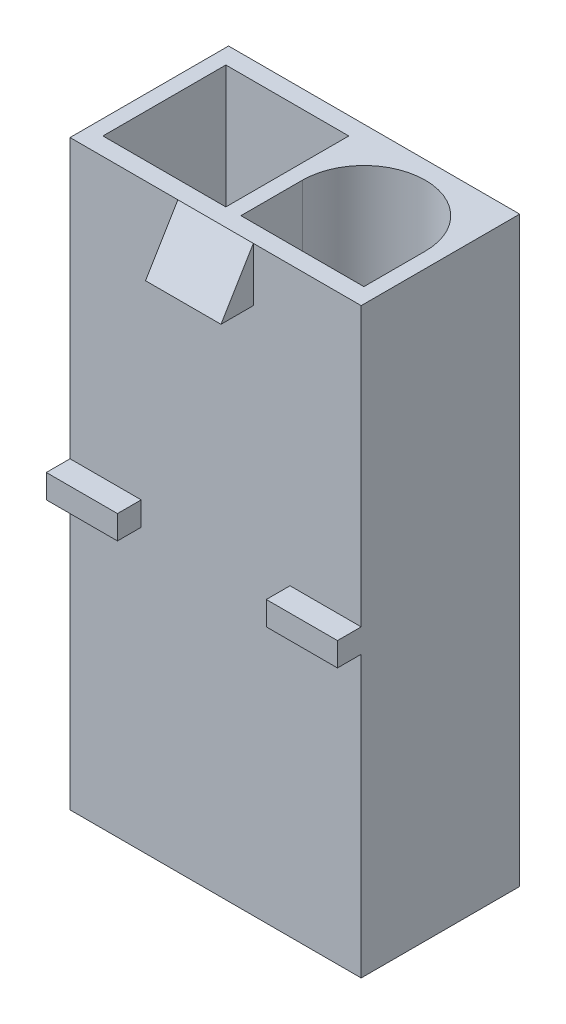
SolidWorks part; units mm, degrees
ref_plane "Front Plane" through (0, 0, 0) normal (0, 0, 1) x (1, 0, 0)
ref_plane "Top Plane" through (0, 0, 0) normal (0, 1, 0) x (1, 0, 0)
ref_plane "Right Plane" through (0, 0, 0) normal (1, 0, 0) x (0, 0, -1)
sketch "Sketch1" plane through (0, 0, 0) normal (0, 0, 1) x (1, 0, 0)
  line L1 (-6.75, -13.5) -> (6.75, -13.5)
  line L2 (-6.75, -13.5) -> (-6.75, 13.5)
  line L3 (-6.75, 13.5) -> (6.75, 13.5)
  line L4 (6.75, -13.5) -> (6.75, 13.5)
  line L5 (-6.75, -13.5) -> (6.75, 13.5) construction
  line L6 (-6.75, 13.5) -> (6.75, -13.5) construction
  point P0 (0, 0)
  dimension "D1" = 27
  dimension "D2" = 13.5
extrude "Main" add sketch "Sketch1" along normal mid plane 7.35
sketch "Sketch2" plane through (0, -13.5, 0) normal (0, -1, 0) x (-1, 0, 0)
  circle A0 centre (3, 0) radius 2.75
  circle A1 centre (-3, 0) radius 2.75
  point P4 (0, 0)
  dimension "D1" = 5.5
  dimension "D2" = 3
  dimension "D3" = 3
extrude "BackCableHole" cut sketch "Sketch2" against normal blind 8.5
sketch "Sketch3" plane through (0, 13.5, 0) normal (0, 1, 0) x (1, 0, 0)
  line L0 (-6.75, -3.675) -> (-6.75, 3.675) construction
  line L1 (-6.05, -2.85) -> (-0.35, -2.85)
  line L2 (-6.05, -2.85) -> (-6.05, 2.85)
  line L3 (-6.05, 2.85) -> (-0.35, 2.85)
  line L4 (-0.35, -2.85) -> (-0.35, 2.85)
  line L5 (6.05, -2.85) -> (0.35, -2.85)
  line L6 (6.05, -2.85) -> (6.05, 0)
  line L7 (6.75, -3.675) -> (6.75, 3.675) construction
  line L8 (0.35, -2.85) -> (0.35, 0)
  line L9 (-0.35, 2.85) -> (6.05, 2.85) construction
  arc A0 (6.05, 0) -> (0.35, 0) centre (3.2, 0) ccw
  point P9 (-6.05, 0)
  dimension "D1" = 5.7
  dimension "D2" = 5.7
  dimension "D3" = 0.7
  dimension "D4" = 0.7
extrude "FrontConnectorHole" cut sketch "Sketch3" against normal blind 8.5
sketch "Sketch4" plane through (0, 0, 0) normal (1, 0, 0) x (0, 0, -1)
  line L0 (-3.675, 13.5) -> (-5.175, 11)
  line L1 (-5.175, 11) -> (-3.675, 11)
  line L2 (-3.675, 13.5) -> (-3.675, -13.5) construction
  line L3 (-3.675, 11) -> (-3.675, 13.5)
  dimension "D1" = 1.5
  dimension "D2" = 2.5
extrude "MainHook" add sketch "Sketch4" along normal mid plane 3.5
sketch "Sketch5" plane through (0, 0, 0) normal (1, 0, 0) x (0, 0, -1)
  line L0 (3.675, -13.5) -> (3.675, 13.5) construction
  line L1 (3.675, 0.9) -> (4.775, 0.9)
  line L2 (3.675, 0.9) -> (3.675, -0.2)
  line L3 (3.675, -0.2) -> (4.775, -0.2)
  line L4 (4.775, 0.9) -> (4.775, -0.2)
  line L5 (-3.675, -13.5) -> (3.675, -13.5) construction
  dimension "D1" = 1.1
  dimension "D2" = 1.1
  dimension "D3" = 13.3
extrude "BottomLine" add sketch "Sketch5" along normal mid plane 9
sketch "Sketch6" plane through (0, 0, 3.675) normal (0, 0, 1) x (1, 0, 0)
  line L0 (-6.75, 13.5) -> (-6.75, -13.5) construction
  line L1 (-6.75, 0.6) -> (-3.45, 0.6)
  line L2 (-6.75, 0.6) -> (-6.75, -0.5)
  line L3 (-6.75, -0.5) -> (-3.45, -0.5)
  line L4 (-3.45, 0.6) -> (-3.45, -0.5)
  line L5 (6.75, -13.5) -> (6.75, 13.5) construction
  line L6 (3.45, 0.6) -> (6.75, 0.6)
  line L7 (3.45, 0.6) -> (3.45, -0.5)
  line L8 (3.45, -0.5) -> (6.75, -0.5)
  line L9 (6.75, 0.6) -> (6.75, -0.5)
  line L10 (-6.75, -13.5) -> (6.75, -13.5) construction
  dimension "D1" = 3.3
  dimension "D2" = 1.1
  dimension "D3" = 13
extrude "SideHook" add sketch "Sketch6" along normal blind 1.1
